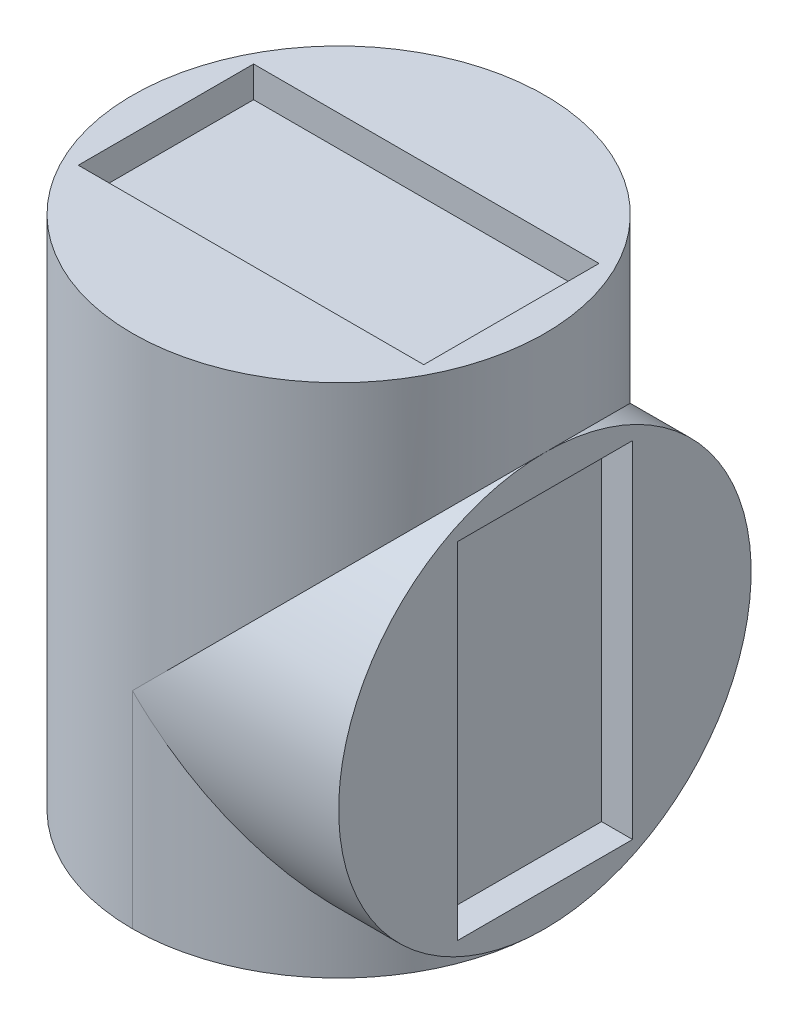
SolidWorks part; units mm, degrees
ref_plane "Alzado" through (0, 0, 0) normal (0, 0, 1) x (1, 0, 0)
ref_plane "Planta" through (0, 0, 0) normal (0, 1, 0) x (1, 0, 0)
ref_plane "Vista lateral" through (0, 0, 0) normal (1, 0, 0) x (0, 0, -1)
sketch "Croquis1" plane through (0, 0, 0) normal (0, 1, 0) x (1, 0, 0)
  circle A0 centre (0, 0) radius 20
  dimension "D1" = 40
extrude "Saliente-Extruir1" add sketch "Croquis1" along normal blind 50
sketch "Croquis3" plane through (0, 0, 0) normal (1, 0, 0) x (0, 0, -1)
  line L0 (0, 50) -> (0, 0) construction
  line L2 (-20, 0) -> (20, 0) construction
  circle A0 centre (0, 20) radius 20
  dimension "D1" = 40
extrude "Saliente-Extruir2" add sketch "Croquis3" along normal blind 20
sketch "Croquis4" plane through (0, 50, 0) normal (0, 1, 0) x (1, 0, 0)
  line L1 (-16.75, -8.5) -> (16.75, -8.5)
  line L2 (-16.75, -8.5) -> (-16.75, 8.5)
  line L3 (-16.75, 8.5) -> (16.75, 8.5)
  line L4 (16.75, -8.5) -> (16.75, 8.5)
  line L5 (-16.75, -8.5) -> (16.75, 8.5) construction
  line L6 (-16.75, 8.5) -> (16.75, -8.5) construction
  point P0 (0, 0)
  dimension "D1" = 17
  dimension "D2" = 33.5
extrude "Cortar-Extruir2" cut sketch "Croquis4" against normal blind 3
sketch "Croquis5" plane through (20, 0, 0) normal (1, 0, 0) x (0, 0, -1)
  line L0 (0, 0) -> (0, 20) construction
  line L1 (-8.5, 36.75) -> (8.5, 36.75)
  line L2 (-8.5, 36.75) -> (-8.5, 3.25)
  line L3 (-8.5, 3.25) -> (8.5, 3.25)
  line L4 (8.5, 36.75) -> (8.5, 3.25)
  line L5 (-8.5, 36.75) -> (8.5, 3.25) construction
  line L6 (-8.5, 3.25) -> (8.5, 36.75) construction
  line L7 (-20, 20) -> (0, 20) construction
  point P0 (0, 20)
  dimension "D1" = 33.5
  dimension "D2" = 17
extrude "Cortar-Extruir3" cut sketch "Croquis5" against normal blind 3
